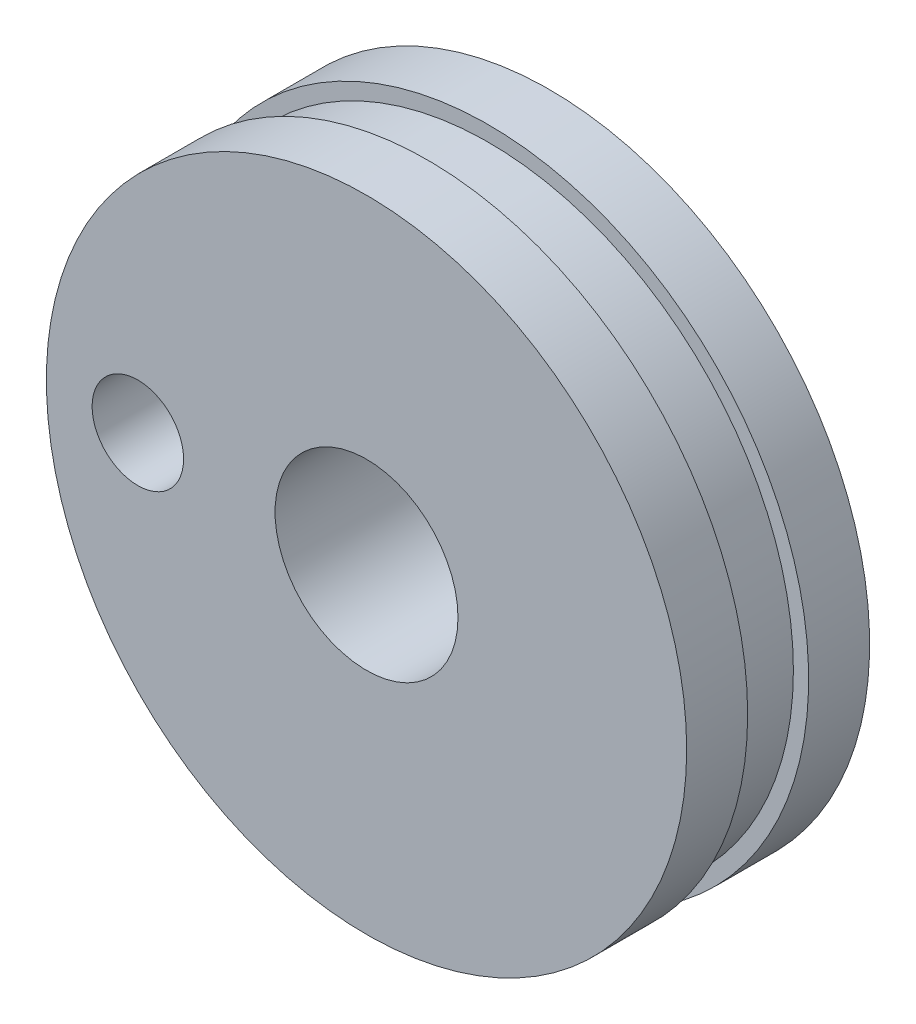
SolidWorks part; units mm, degrees
ref_plane "Alzado" through (0, 0, 0) normal (0, 0, 1) x (1, 0, 0)
ref_plane "Planta" through (0, 0, 0) normal (0, 1, 0) x (1, 0, 0)
ref_plane "Vista lateral" through (0, 0, 0) normal (1, 0, 0) x (0, 0, -1)
sketch "Croquis2" plane through (0, 0, 0) normal (0, 0, 1) x (1, 0, 0)
  circle A0 centre (0, 0) radius 73.5
  dimension "D1" = 147
extrude "Saliente-Extruir1" add sketch "Croquis2" along normal blind 14
sketch "Croquis6" plane through (0, 0, 0) normal (0, 0, 1) x (1, 0, 0)
  circle A0 centre (0, 0) radius 70
  dimension "D1" = 140
extrude "Saliente-Extruir4" add sketch "Croquis6" against normal blind 14
sketch "Croquis7" plane through (0, 0, 0) normal (0, 0, 1) x (1, 0, 0)
  circle A0 centre (0, 0) radius 73.5
  dimension "D1" = 147
sketch "Croquis8" plane through (0, 0, -14) normal (0, 0, -1) x (-1, 0, 0)
  circle A0 centre (0, 0) radius 73.5
  dimension "D1" = 147
extrude "Saliente-Extruir5" add sketch "Croquis8" along normal blind 14
sketch "Croquis10" plane through (0, 0, 14) normal (0, 0, 1) x (1, 0, 0)
  circle A0 centre (0, 0) radius 21
  dimension "D1" = 42
extrude "Cortar-Extruir2" cut sketch "Croquis10" against normal blind 84
sketch "Croquis11" plane through (0, 0, -28) normal (0, 0, -1) x (-1, 0, 0)
  line L0 (21, 0) -> (42, 0) construction
  line L1 (73.5, 0) -> (66.5, 0) construction
  circle A0 centre (0, 0) radius 21 construction
  circle A1 centre (0, 0) radius 73.5 construction
  circle A2 centre (52.5, 0) radius 10.5
  dimension "D3" = 21
  dimension "D1" = 21
  dimension "D2" = 7
  dimension "D4" = 14
extrude "Cortar-Extruir3" cut sketch "Croquis11" against normal blind 84
